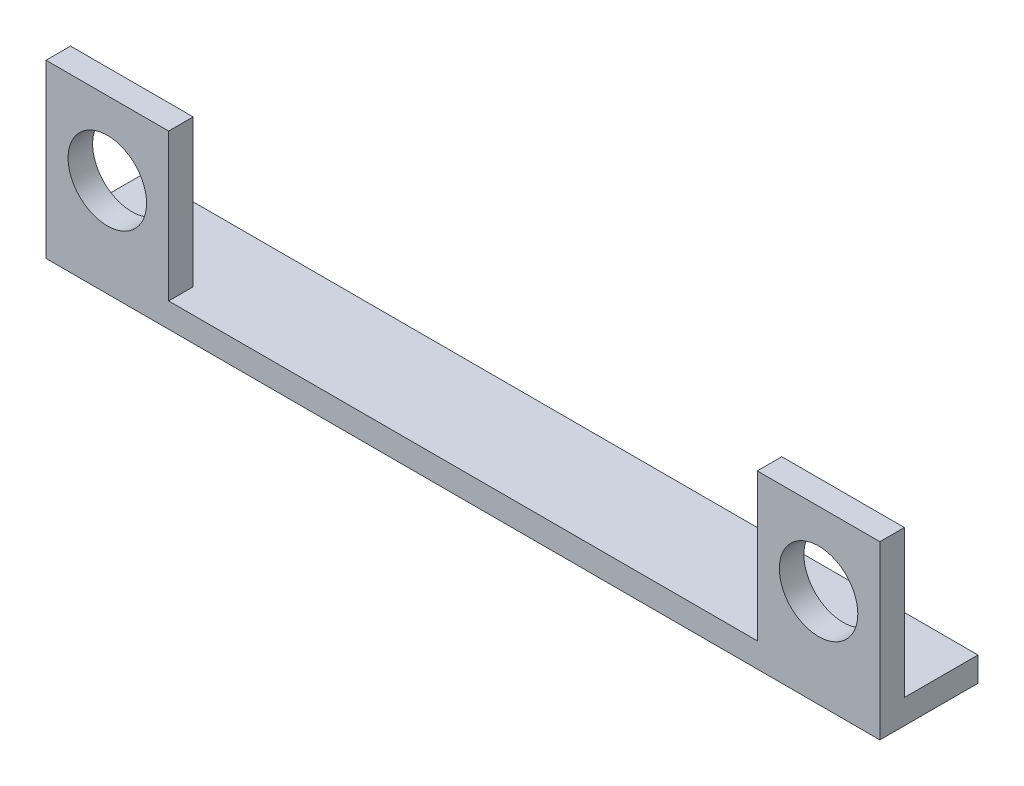
SolidWorks part; units mm, degrees
ref_plane "Front Plane" through (0, 0, 0) normal (0, 0, 1) x (1, 0, 0)
ref_plane "Top Plane" through (0, 0, 0) normal (0, 1, 0) x (1, 0, 0)
ref_plane "Right Plane" through (0, 0, 0) normal (1, 0, 0) x (0, 0, -1)
sketch "Sketch1" plane through (0, 0, 0) normal (0, 1, 0) x (1, 0, 0)
  line L1 (-17, 2) -> (17, 2)
  line L2 (-17, 2) -> (-17, -2)
  line L3 (-17, -2) -> (17, -2)
  line L4 (17, 2) -> (17, -2)
  dimension "D1" = 34
  dimension "D2" = 4
  dimension "D3" = 2
  dimension "D4" = 17
extrude "Boss-Extrude1" add sketch "Sketch1" along normal blind 1
sketch "Sketch2" plane through (0, 1, 0) normal (0, 1, 0) x (1, 0, 0)
  line L1 (-17, -2) -> (-12, -2)
  line L2 (-17, -2) -> (-17, -1)
  line L3 (-17, -1) -> (-12, -1)
  line L4 (-12, -2) -> (-12, -1)
  line L5 (17, -2) -> (12, -2)
  line L6 (17, -2) -> (17, -1)
  line L7 (17, -1) -> (12, -1)
  line L8 (12, -2) -> (12, -1)
  dimension "D1" = 1
  dimension "D2" = 1
  dimension "D3" = 5
  dimension "D4" = 5
extrude "Boss-Extrude2" add sketch "Sketch2" along normal blind 6
sketch "Sketch3" plane through (0, 0, 2) normal (0, 0, 1) x (1, 0, 0)
  circle A0 centre (-14.5, 4) radius 1.6
  circle A1 centre (14.5, 4) radius 1.6
  dimension "D3" = 3.2
  dimension "D4" = 3.2
  dimension "D1" = 4
  dimension "D2" = 4
  dimension "D5" = 14.5
  dimension "D6" = 14.5
extrude "Cut-Extrude1" cut sketch "Sketch3" against normal blind 6
